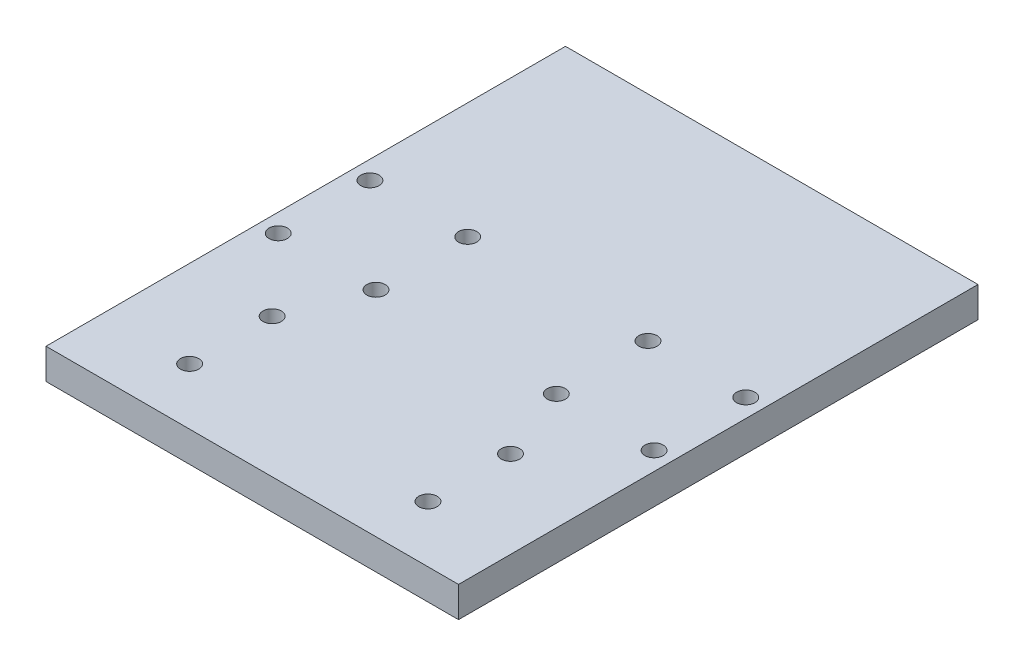
SolidWorks part; units mm, degrees
ref_plane "Front Plane" through (0, 0, 0) normal (0, 0, 1) x (1, 0, 0)
ref_plane "Top Plane" through (0, 0, 0) normal (0, 1, 0) x (1, 0, 0)
ref_plane "Right Plane" through (0, 0, 0) normal (1, 0, 0) x (0, 0, -1)
sketch "Sketch1" plane through (0, 0, 0) normal (0, 1, 0) x (1, 0, 0)
  line L1 (-33, -42.5) -> (33, -42.5)
  line L2 (-33, -42.5) -> (-33, 42.5)
  line L3 (-33, 42.5) -> (33, 42.5)
  line L4 (33, -42.5) -> (33, 42.5)
  line L5 (-33, -42.5) -> (33, 42.5) construction
  line L6 (-33, 42.5) -> (33, -42.5) construction
  point P0 (0, 0)
  dimension "D1" = 66
  dimension "D2" = 85
extrude "Boss-Extrude1" add sketch "Sketch1" along normal blind 5
sketch "Sketch2" plane through (0, 5, 0) normal (0, 1, 0) x (1, 0, 0)
  line L0 (-29.5, 42.5) -> (-29.5, -42.5) construction
  line L4 (33, 42.5) -> (-33, 42.5) construction
  line L5 (-33, -42.5) -> (33, -42.5) construction
  line L6 (-33, 42.5) -> (-33, -42.5) construction
  line L7 (0, 0) -> (0, 15.1289) construction
  circle A2 centre (-29.5, 21.25) radius 1.5
  circle A3 centre (-29.5, -21.25) radius 1.5
  circle A4 centre (29.5, -21.25) radius 1.5
  circle A5 centre (29.5, 21.25) radius 1.5
  dimension "D2" = 3
  dimension "D3" = 3
  dimension "D1" = 3.5
  dimension "D4" = 21.25
  dimension "D5" = 21.25
sketch "Sketch4" plane through (0, 5, 0) normal (0, 1, 0) x (1, 0, 0)
  line L0 (0, 0) -> (0, -13.5692) construction
  circle A0 centre (-30.75, 7.5) radius 1.5
  circle A1 centre (-14.75, 7.5) radius 1.5
  circle A2 centre (-30.75, -7.5) radius 1.5
  circle A3 centre (-14.75, -7.5) radius 1.5
  circle A4 centre (14.75, -7.5) radius 1.5
  circle A5 centre (30.75, -7.5) radius 1.5
  circle A6 centre (14.75, 7.5) radius 1.5
  circle A7 centre (30.75, 7.5) radius 1.5
  dimension "D1" = 3
  dimension "D3" = 3
  dimension "D4" = 3
  dimension "D6" = 3
  dimension "D2" = 7.5
  dimension "D5" = 15
  dimension "D7" = 16
  dimension "D8" = 14.75
extrude "Cut-Extrude2" cut sketch "Sketch4" against normal blind 10 contours A0 | A1 | A2 | A3 | A6 | A4 | A7 | A5
sketch "Sketch5" plane through (-33, 0, 0) normal (-1, 0, 0) x (0, 0, 1)
  line L0 (0, 0) -> (0, 5) construction
  line L1 (-42.5, 0) -> (42.5, 0) construction
  line L2 (-42.5, 5) -> (42.5, 5) construction
  line L3 (-8.5, 0) -> (8.5, 0)
  line L5 (-8.5, 0) -> (8.5, 0)
  line L6 (-8.5, 0) -> (-8.5, 5)
  line L7 (-8.5, 5) -> (8.5, 5)
  line L8 (8.5, 0) -> (8.5, 5)
  point P8 (0, 0)
  dimension "D1" = 17
sketch "Sketch6" plane through (0, 5, 0) normal (0, 1, 0) x (1, 0, 0)
  line L0 (0, 0) -> (-4.372, 0) construction
  line L1 (0, 0) -> (0, 6.2978) construction
  line L2 (-33, 42.5) -> (-33, -42.5) construction
  circle A0 centre (-19.5, -26.5) radius 1.5
  circle A2 centre (-14.75, -7.5) radius 1.5 construction
  circle A3 centre (19.5, -26.5) radius 1.5
  circle A4 centre (19.5, 26.5) radius 1.5
  circle A5 centre (-19.5, 26.5) radius 1.5
  dimension "D1" = 3
  dimension "D2" = 13.5
  dimension "D3" = 19
sketch "Sketch7" plane through (0, 5, 0) normal (0, 1, 0) x (1, 0, 0)
  line L0 (-33, -15) -> (33, -15) construction
  line L1 (-33, 42.5) -> (-33, -42.5) construction
  line L2 (33, -42.5) -> (33, 42.5) construction
  circle A0 centre (-14.75, -7.5) radius 1.5 construction
  dimension "D1" = 7.5
sketch "Sketch8" plane through (-33, 0, 0) normal (-1, 0, 0) x (0, 0, 1)
  line L1 (-42.5, 5) -> (42.5, 5)
  line L2 (-42.5, 5) -> (-42.5, 0)
  line L3 (-42.5, 0) -> (42.5, 0)
  line L4 (42.5, 5) -> (42.5, 0)
extrude "Boss-Extrude2" add sketch "Sketch8" along normal blind 0.75
sketch "Sketch9" plane through (33, 0, 0) normal (1, 0, 0) x (0, 0, -1)
  line L1 (-42.5, 5) -> (42.5, 5)
  line L2 (-42.5, 5) -> (-42.5, 0)
  line L3 (-42.5, 0) -> (42.5, 0)
  line L4 (42.5, 5) -> (42.5, 0)
extrude "Boss-Extrude3" add sketch "Sketch9" along normal blind 0.75
sketch "Sketch10" plane through (0, 5, 0) normal (0, 1, 0) x (1, 0, 0)
  line L0 (-19.5, -42.5) -> (-19.5, -31.2042) construction
  line L1 (-33.75, -42.5) -> (33.75, -42.5) construction
  line L2 (-33.75, -42.5) -> (-33.75, 42.5) construction
  line L3 (0, -42.5) -> (0, -31.2042) construction
  circle A0 centre (-19.5, -33.25) radius 1.5
  circle A1 centre (-19.5, -19.75) radius 1.5
  circle A2 centre (19.5, -33.25) radius 1.5
  circle A3 centre (19.5, -19.75) radius 1.5
  dimension "D2" = 3
  dimension "D4" = 3
  dimension "D1" = 14.25
  dimension "D3" = 9.25
  dimension "D5" = 13.5
extrude "Cut-Extrude3" cut sketch "Sketch10" against normal blind 10
